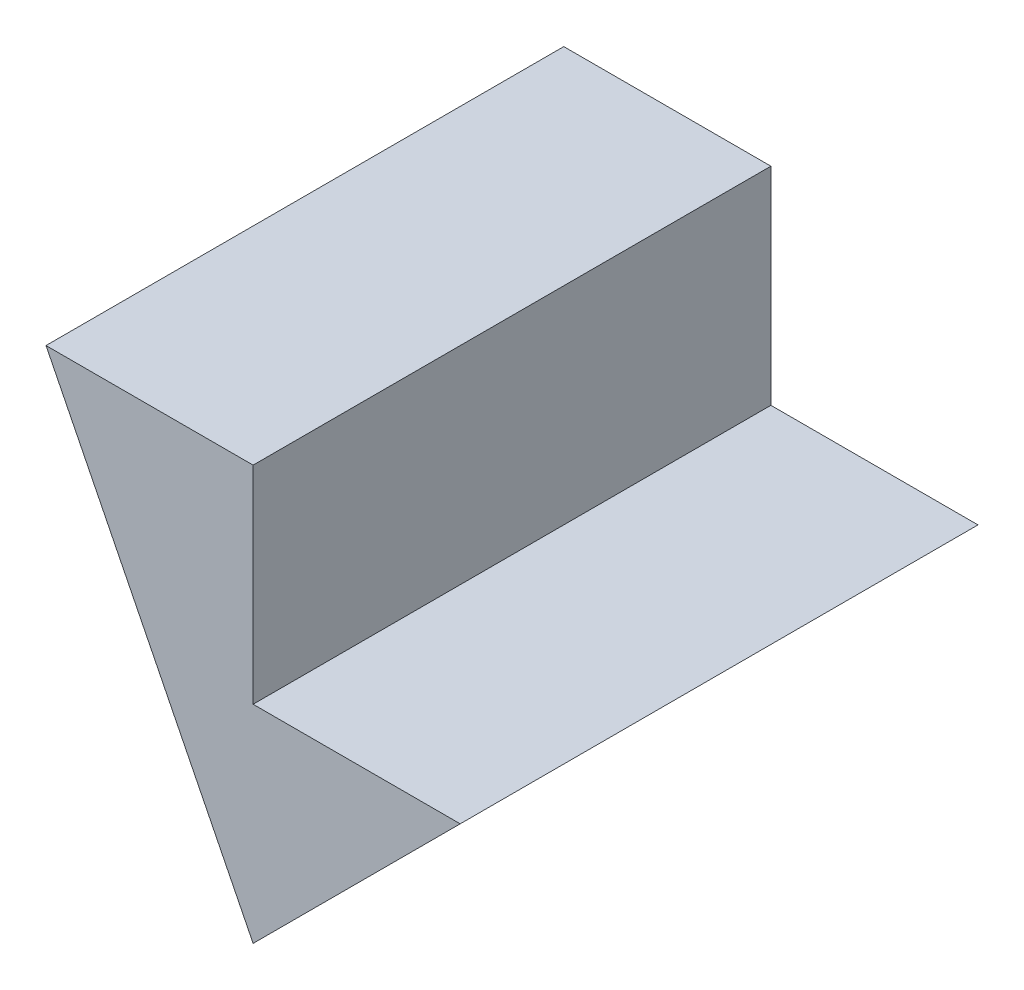
SolidWorks part; units mm, degrees
ref_plane "Front Plane" through (0, 0, 0) normal (0, 0, 1) x (1, 0, 0)
ref_plane "Top Plane" through (0, 0, 0) normal (0, 1, 0) x (1, 0, 0)
ref_plane "Right Plane" through (0, 0, 0) normal (1, 0, 0) x (0, 0, -1)
sketch "Sketch1" plane through (0, 0, 0) normal (0, 0, 1) x (1, 0, 0)
  line L0 (-10, 0) -> (0, 0)
  line L1 (0, 0) -> (0, -10)
  line L2 (0, -10) -> (10, -10)
  line L3 (10, -10) -> (0, -20)
  line L4 (0, -20) -> (-10, 0)
  point P2 (10, -20)
  point P6 (-10, -20)
  dimension "D1" = 10
  dimension "D2" = 10
  dimension "D3" = 10
  dimension "D4" = 10
  dimension "D5" = 10
  dimension "D6" = 20
  dimension "D7" = 10
  dimension "D8" = 20
extrude "Boss-Extrude2" add sketch "Sketch1" along normal blind 25
